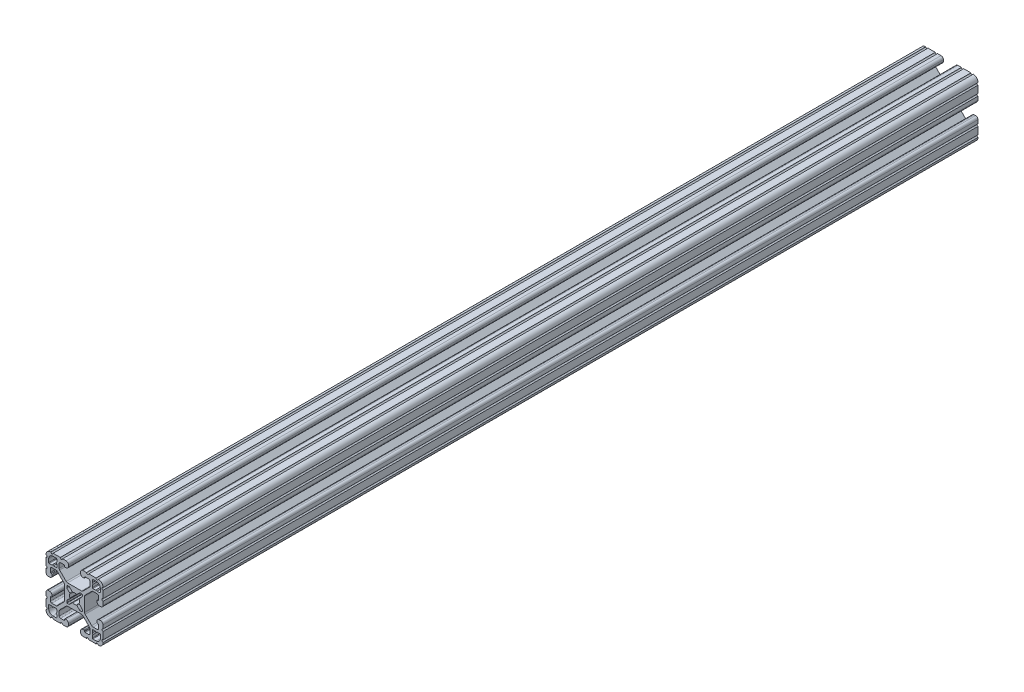
SolidWorks part; units mm, degrees
ref_plane "Front Plane" through (0, 0, 0) normal (0, 0, 1) x (1, 0, 0)
ref_plane "Top Plane" through (0, 0, 0) normal (0, 1, 0) x (1, 0, 0)
ref_plane "Right Plane" through (0, 0, 0) normal (1, 0, 0) x (0, 0, -1)
ref_plane "Plane1" through (0, 0, -2322.576) normal (0, 0, -1) x (-1, 0, 0)
sketch "Sketch1" plane through (0, 0, -2322.576) normal (0, 0, -1) x (-1, 0, 0)
  line L0 (17.2466, 14.4526) -> (17.2466, 12.2428)
  line L1 (16.8656, 11.8618) -> (15.0927, 11.8618)
  line L2 (15.0927, 11.8618) -> (14.5542, 12.4003)
  line L3 (14.5542, 12.4003) -> (14.0157, 11.8618)
  line L4 (14.0157, 11.8618) -> (12.2428, 11.8618)
  line L5 (11.8618, 12.2428) -> (11.8618, 14.0157)
  line L6 (11.8618, 14.0157) -> (12.4003, 14.5542)
  line L7 (12.4003, 14.5542) -> (11.8618, 15.0927)
  line L8 (11.8618, 15.0927) -> (11.8618, 16.8656)
  line L9 (12.2428, 17.2466) -> (14.4526, 17.2466)
  line L10 (17.2466, -12.2428) -> (17.2466, -14.4526)
  line L11 (14.4526, -17.2466) -> (12.2428, -17.2466)
  line L12 (11.8618, -16.8656) -> (11.8618, -15.0927)
  line L13 (11.8618, -15.0927) -> (12.4003, -14.5542)
  line L14 (12.4003, -14.5542) -> (11.8618, -14.0157)
  line L15 (11.8618, -14.0157) -> (11.8618, -12.2428)
  line L16 (12.2428, -11.8618) -> (14.0157, -11.8618)
  line L17 (14.0157, -11.8618) -> (14.5542, -12.4003)
  line L18 (14.5542, -12.4003) -> (15.0927, -11.8618)
  line L19 (15.0927, -11.8618) -> (16.8656, -11.8618)
  line L20 (5.1689, -3.9207) -> (5.1689, -4.9149)
  line L21 (4.9149, -5.1689) -> (3.9207, -5.1689)
  line L22 (3.2921, -4.9085) -> (1.5823, -3.1988)
  line L23 (-1.5823, -3.1988) -> (-3.2921, -4.9085)
  line L24 (-3.9207, -5.1689) -> (-4.9149, -5.1689)
  line L25 (-5.1689, -4.9149) -> (-5.1689, -3.9207)
  line L26 (-4.9085, -3.2921) -> (-3.1988, -1.5823)
  line L27 (-3.1988, 1.5823) -> (-4.9085, 3.2921)
  line L28 (-5.1689, 3.9207) -> (-5.1689, 4.9149)
  line L29 (-4.9149, 5.1689) -> (-3.9207, 5.1689)
  line L30 (-3.2921, 4.9085) -> (-1.5823, 3.1988)
  line L31 (1.5823, 3.1988) -> (3.2921, 4.9085)
  line L32 (3.9207, 5.1689) -> (4.9149, 5.1689)
  line L33 (5.1689, 4.9149) -> (5.1689, 3.9207)
  line L34 (4.9085, 3.2921) -> (3.1988, 1.5823)
  line L35 (3.1988, -1.5823) -> (4.9085, -3.2921)
  line L36 (-11.8618, -12.2428) -> (-11.8618, -14.0157)
  line L37 (-11.8618, -14.0157) -> (-12.4003, -14.5542)
  line L38 (-12.4003, -14.5542) -> (-11.8618, -15.0927)
  line L39 (-11.8618, -15.0927) -> (-11.8618, -16.8656)
  line L40 (-12.2428, -17.2466) -> (-14.4526, -17.2466)
  line L41 (-17.2466, -14.4526) -> (-17.2466, -12.2428)
  line L42 (-16.8656, -11.8618) -> (-15.0927, -11.8618)
  line L43 (-15.0927, -11.8618) -> (-14.5542, -12.4003)
  line L44 (-14.5542, -12.4003) -> (-14.0157, -11.8618)
  line L45 (-14.0157, -11.8618) -> (-12.2428, -11.8618)
  line L46 (-11.8618, 16.8656) -> (-11.8618, 15.0927)
  line L47 (-11.8618, 15.0927) -> (-12.4003, 14.5542)
  line L48 (-12.4003, 14.5542) -> (-11.8618, 14.0157)
  line L49 (-11.8618, 14.0157) -> (-11.8618, 12.2428)
  line L50 (-12.2428, 11.8618) -> (-14.0157, 11.8618)
  line L51 (-14.0157, 11.8618) -> (-14.5542, 12.4003)
  line L52 (-14.5542, 12.4003) -> (-15.0927, 11.8618)
  line L53 (-15.0927, 11.8618) -> (-16.8656, 11.8618)
  line L54 (-17.2466, 12.2428) -> (-17.2466, 14.4526)
  line L55 (-14.4526, 17.2466) -> (-12.2428, 17.2466)
  line L56 (19.05, -14.3256) -> (19.05, -9.4996)
  line L57 (19.05, -7.9756) -> (19.05, -5.6388)
  line L58 (17.4752, -4.064) -> (16.5608, -4.064)
  line L59 (14.986, -5.6388) -> (14.986, -6.35)
  line L60 (15.367, -6.731) -> (15.6972, -6.731)
  line L61 (16.0782, -7.112) -> (16.0782, -9.398)
  line L62 (15.1892, -10.287) -> (12.3756, -10.287)
  line L63 (11.4776, -9.915) -> (7.1157, -5.5531)
  line L64 (6.7437, -4.6551) -> (6.7437, 4.6551)
  line L65 (7.1157, 5.5531) -> (11.4776, 9.915)
  line L66 (12.3756, 10.287) -> (15.1892, 10.287)
  line L67 (16.0782, 9.398) -> (16.0782, 7.112)
  line L68 (15.6972, 6.731) -> (15.367, 6.731)
  line L69 (14.986, 6.35) -> (14.986, 5.6388)
  line L70 (16.5608, 4.064) -> (17.4752, 4.064)
  line L71 (19.05, 5.6388) -> (19.05, 7.9756)
  line L72 (19.05, 9.4996) -> (19.05, 14.3256)
  line L73 (14.3256, 19.05) -> (9.4996, 19.05)
  line L74 (7.9756, 19.05) -> (5.6388, 19.05)
  line L75 (4.064, 17.4752) -> (4.064, 16.5608)
  line L76 (5.6388, 14.986) -> (6.35, 14.986)
  line L77 (6.731, 15.367) -> (6.731, 15.6972)
  line L78 (7.112, 16.0782) -> (9.398, 16.0782)
  line L79 (10.287, 15.1892) -> (10.287, 12.3756)
  line L80 (9.915, 11.4776) -> (5.5531, 7.1157)
  line L81 (4.6551, 6.7437) -> (-4.6551, 6.7437)
  line L82 (-5.5531, 7.1157) -> (-9.915, 11.4776)
  line L83 (-10.287, 12.3756) -> (-10.287, 15.1892)
  line L84 (-9.398, 16.0782) -> (-7.112, 16.0782)
  line L85 (-6.731, 15.6972) -> (-6.731, 15.367)
  line L86 (-6.35, 14.986) -> (-5.6388, 14.986)
  line L87 (-4.064, 16.5608) -> (-4.064, 17.4752)
  line L88 (-5.6388, 19.05) -> (-7.9756, 19.05)
  line L89 (-9.4996, 19.05) -> (-14.3256, 19.05)
  line L90 (-19.05, 14.3256) -> (-19.05, 9.4996)
  line L91 (-19.05, 7.9756) -> (-19.05, 5.6388)
  line L92 (-17.4752, 4.064) -> (-16.5608, 4.064)
  line L93 (-14.986, 5.6388) -> (-14.986, 6.35)
  line L94 (-15.367, 6.731) -> (-15.6972, 6.731)
  line L95 (-16.0782, 7.112) -> (-16.0782, 9.398)
  line L96 (-15.1892, 10.287) -> (-12.3756, 10.287)
  line L97 (-11.4776, 9.915) -> (-7.1157, 5.5531)
  line L98 (-6.7437, 4.6551) -> (-6.7437, -4.6551)
  line L99 (-7.1157, -5.5531) -> (-11.4776, -9.915)
  line L100 (-12.3756, -10.287) -> (-15.1892, -10.287)
  line L101 (-16.0782, -9.398) -> (-16.0782, -7.112)
  line L102 (-15.6972, -6.731) -> (-15.367, -6.731)
  line L103 (-14.986, -6.35) -> (-14.986, -5.6388)
  line L104 (-16.5608, -4.064) -> (-17.4752, -4.064)
  line L105 (-19.05, -5.6388) -> (-19.05, -7.9756)
  line L106 (-19.05, -9.4996) -> (-19.05, -14.3256)
  line L107 (-14.3256, -19.05) -> (-9.4996, -19.05)
  line L108 (-7.9756, -19.05) -> (-5.6388, -19.05)
  line L109 (-4.064, -17.4752) -> (-4.064, -16.5608)
  line L110 (-5.6388, -14.986) -> (-6.35, -14.986)
  line L111 (-6.731, -15.367) -> (-6.731, -15.6972)
  line L112 (-7.112, -16.0782) -> (-9.398, -16.0782)
  line L113 (-10.287, -15.1892) -> (-10.287, -12.3756)
  line L114 (-9.915, -11.4776) -> (-5.5531, -7.1157)
  line L115 (-4.6551, -6.7437) -> (4.6551, -6.7437)
  line L116 (5.5531, -7.1157) -> (9.915, -11.4776)
  line L117 (10.287, -12.3756) -> (10.287, -15.1892)
  line L118 (9.398, -16.0782) -> (7.112, -16.0782)
  line L119 (6.731, -15.6972) -> (6.731, -15.367)
  line L120 (6.35, -14.986) -> (5.6388, -14.986)
  line L121 (4.064, -16.5608) -> (4.064, -17.4752)
  line L122 (5.6388, -19.05) -> (7.9756, -19.05)
  line L123 (9.4996, -19.05) -> (14.3256, -19.05)
  arc A0 (17.2466, 12.2428) -> (16.8656, 11.8618) centre (16.8656, 12.2428) cw
  arc A1 (12.2428, 11.8618) -> (11.8618, 12.2428) centre (12.2428, 12.2428) cw
  arc A2 (11.8618, 16.8656) -> (12.2428, 17.2466) centre (12.2428, 16.8656) cw
  arc A3 (14.4526, 17.2466) -> (17.2466, 14.4526) centre (14.4526, 14.4526) cw
  arc A4 (17.2466, -14.4526) -> (14.4526, -17.2466) centre (14.4526, -14.4526) cw
  arc A5 (12.2428, -17.2466) -> (11.8618, -16.8656) centre (12.2428, -16.8656) cw
  arc A6 (11.8618, -12.2428) -> (12.2428, -11.8618) centre (12.2428, -12.2428) cw
  arc A7 (16.8656, -11.8618) -> (17.2466, -12.2428) centre (16.8656, -12.2428) cw
  arc A8 (5.1689, -4.9149) -> (4.9149, -5.1689) centre (4.9149, -4.9149) cw
  arc A9 (3.9207, -5.1689) -> (3.2921, -4.9085) centre (3.9207, -4.2799) cw
  arc A10 (1.5823, -3.1988) -> (1.178, -3.1119) centre (1.3129, -3.4682) ccw
  arc A11 (1.178, -3.1119) -> (-1.178, -3.1119) centre (0, 0) cw
  arc A12 (-1.178, -3.1119) -> (-1.5823, -3.1988) centre (-1.3129, -3.4682) ccw
  arc A13 (-3.2921, -4.9085) -> (-3.9207, -5.1689) centre (-3.9207, -4.2799) cw
  arc A14 (-4.9149, -5.1689) -> (-5.1689, -4.9149) centre (-4.9149, -4.9149) cw
  arc A15 (-5.1689, -3.9207) -> (-4.9085, -3.2921) centre (-4.2799, -3.9207) cw
  arc A16 (-3.1988, -1.5823) -> (-3.1119, -1.178) centre (-3.4682, -1.3129) ccw
  arc A17 (-3.1119, -1.178) -> (-3.1119, 1.178) centre (0, 0) cw
  arc A18 (-3.1119, 1.178) -> (-3.1988, 1.5823) centre (-3.4682, 1.3129) ccw
  arc A19 (-4.9085, 3.2921) -> (-5.1689, 3.9207) centre (-4.2799, 3.9207) cw
  arc A20 (-5.1689, 4.9149) -> (-4.9149, 5.1689) centre (-4.9149, 4.9149) cw
  arc A21 (-3.9207, 5.1689) -> (-3.2921, 4.9085) centre (-3.9207, 4.2799) cw
  arc A22 (-1.5823, 3.1988) -> (-1.178, 3.1119) centre (-1.3129, 3.4682) ccw
  arc A23 (-1.178, 3.1119) -> (1.178, 3.1119) centre (0, 0) cw
  arc A24 (1.178, 3.1119) -> (1.5823, 3.1988) centre (1.3129, 3.4682) ccw
  arc A25 (3.2921, 4.9085) -> (3.9207, 5.1689) centre (3.9207, 4.2799) cw
  arc A26 (4.9149, 5.1689) -> (5.1689, 4.9149) centre (4.9149, 4.9149) cw
  arc A27 (5.1689, 3.9207) -> (4.9085, 3.2921) centre (4.2799, 3.9207) cw
  arc A28 (3.1988, 1.5823) -> (3.1119, 1.178) centre (3.4682, 1.3129) ccw
  arc A29 (3.1119, 1.178) -> (3.1119, -1.178) centre (0, 0) cw
  arc A30 (3.1119, -1.178) -> (3.1988, -1.5823) centre (3.4682, -1.3129) ccw
  arc A31 (4.9085, -3.2921) -> (5.1689, -3.9207) centre (4.2799, -3.9207) cw
  arc A32 (-11.8618, -16.8656) -> (-12.2428, -17.2466) centre (-12.2428, -16.8656) cw
  arc A33 (-14.4526, -17.2466) -> (-17.2466, -14.4526) centre (-14.4526, -14.4526) cw
  arc A34 (-17.2466, -12.2428) -> (-16.8656, -11.8618) centre (-16.8656, -12.2428) cw
  arc A35 (-12.2428, -11.8618) -> (-11.8618, -12.2428) centre (-12.2428, -12.2428) cw
  arc A36 (-12.2428, 17.2466) -> (-11.8618, 16.8656) centre (-12.2428, 16.8656) cw
  arc A37 (-11.8618, 12.2428) -> (-12.2428, 11.8618) centre (-12.2428, 12.2428) cw
  arc A38 (-16.8656, 11.8618) -> (-17.2466, 12.2428) centre (-16.8656, 12.2428) cw
  arc A39 (-17.2466, 14.4526) -> (-14.4526, 17.2466) centre (-14.4526, 14.4526) cw
  arc A40 (19.05, -9.4996) -> (19.05, -7.9756) centre (19.05, -8.7376) cw
  arc A41 (19.05, -5.6388) -> (17.4752, -4.064) centre (17.4752, -5.6388) ccw
  arc A42 (16.5608, -4.064) -> (14.986, -5.6388) centre (16.5608, -5.6388) ccw
  arc A43 (14.986, -6.35) -> (15.367, -6.731) centre (15.367, -6.35) ccw
  arc A44 (15.6972, -6.731) -> (16.0782, -7.112) centre (15.6972, -7.112) cw
  arc A45 (16.0782, -9.398) -> (15.1892, -10.287) centre (15.1892, -9.398) cw
  arc A46 (12.3756, -10.287) -> (11.4776, -9.915) centre (12.3756, -9.017) cw
  arc A47 (7.1157, -5.5531) -> (6.7437, -4.6551) centre (8.0137, -4.6551) cw
  arc A48 (6.7437, 4.6551) -> (7.1157, 5.5531) centre (8.0137, 4.6551) cw
  arc A49 (11.4776, 9.915) -> (12.3756, 10.287) centre (12.3756, 9.017) cw
  arc A50 (15.1892, 10.287) -> (16.0782, 9.398) centre (15.1892, 9.398) cw
  arc A51 (16.0782, 7.112) -> (15.6972, 6.731) centre (15.6972, 7.112) cw
  arc A52 (15.367, 6.731) -> (14.986, 6.35) centre (15.367, 6.35) ccw
  arc A53 (14.986, 5.6388) -> (16.5608, 4.064) centre (16.5608, 5.6388) ccw
  arc A54 (17.4752, 4.064) -> (19.05, 5.6388) centre (17.4752, 5.6388) ccw
  arc A55 (19.05, 7.9756) -> (19.05, 9.4996) centre (19.05, 8.7376) cw
  arc A56 (19.05, 14.3256) -> (19.0499, 15.8496) centre (19.05, 15.0876) cw
  arc A57 (19.0499, 15.8496) -> (15.8496, 19.0499) centre (15.875, 15.875) ccw
  arc A58 (15.8496, 19.0499) -> (14.3256, 19.05) centre (15.0876, 19.05) cw
  arc A59 (9.4996, 19.05) -> (7.9756, 19.05) centre (8.7376, 19.05) cw
  arc A60 (5.6388, 19.05) -> (4.064, 17.4752) centre (5.6388, 17.4752) ccw
  arc A61 (4.064, 16.5608) -> (5.6388, 14.986) centre (5.6388, 16.5608) ccw
  arc A62 (6.35, 14.986) -> (6.731, 15.367) centre (6.35, 15.367) ccw
  arc A63 (6.731, 15.6972) -> (7.112, 16.0782) centre (7.112, 15.6972) cw
  arc A64 (9.398, 16.0782) -> (10.287, 15.1892) centre (9.398, 15.1892) cw
  arc A65 (10.287, 12.3756) -> (9.915, 11.4776) centre (9.017, 12.3756) cw
  arc A66 (5.5531, 7.1157) -> (4.6551, 6.7437) centre (4.6551, 8.0137) cw
  arc A67 (-4.6551, 6.7437) -> (-5.5531, 7.1157) centre (-4.6551, 8.0137) cw
  arc A68 (-9.915, 11.4776) -> (-10.287, 12.3756) centre (-9.017, 12.3756) cw
  arc A69 (-10.287, 15.1892) -> (-9.398, 16.0782) centre (-9.398, 15.1892) cw
  arc A70 (-7.112, 16.0782) -> (-6.731, 15.6972) centre (-7.112, 15.6972) cw
  arc A71 (-6.731, 15.367) -> (-6.35, 14.986) centre (-6.35, 15.367) ccw
  arc A72 (-5.6388, 14.986) -> (-4.064, 16.5608) centre (-5.6388, 16.5608) ccw
  arc A73 (-4.064, 17.4752) -> (-5.6388, 19.05) centre (-5.6388, 17.4752) ccw
  arc A74 (-7.9756, 19.05) -> (-9.4996, 19.05) centre (-8.7376, 19.05) cw
  arc A75 (-14.3256, 19.05) -> (-15.8496, 19.0499) centre (-15.0876, 19.05) cw
  arc A76 (-15.8496, 19.0499) -> (-19.0499, 15.8496) centre (-15.875, 15.875) ccw
  arc A77 (-19.0499, 15.8496) -> (-19.05, 14.3256) centre (-19.05, 15.0876) cw
  arc A78 (-19.05, 9.4996) -> (-19.05, 7.9756) centre (-19.05, 8.7376) cw
  arc A79 (-19.05, 5.6388) -> (-17.4752, 4.064) centre (-17.4752, 5.6388) ccw
  arc A80 (-16.5608, 4.064) -> (-14.986, 5.6388) centre (-16.5608, 5.6388) ccw
  arc A81 (-14.986, 6.35) -> (-15.367, 6.731) centre (-15.367, 6.35) ccw
  arc A82 (-15.6972, 6.731) -> (-16.0782, 7.112) centre (-15.6972, 7.112) cw
  arc A83 (-16.0782, 9.398) -> (-15.1892, 10.287) centre (-15.1892, 9.398) cw
  arc A84 (-12.3756, 10.287) -> (-11.4776, 9.915) centre (-12.3756, 9.017) cw
  arc A85 (-7.1157, 5.5531) -> (-6.7437, 4.6551) centre (-8.0137, 4.6551) cw
  arc A86 (-6.7437, -4.6551) -> (-7.1157, -5.5531) centre (-8.0137, -4.6551) cw
  arc A87 (-11.4776, -9.915) -> (-12.3756, -10.287) centre (-12.3756, -9.017) cw
  arc A88 (-15.1892, -10.287) -> (-16.0782, -9.398) centre (-15.1892, -9.398) cw
  arc A89 (-16.0782, -7.112) -> (-15.6972, -6.731) centre (-15.6972, -7.112) cw
  arc A90 (-15.367, -6.731) -> (-14.986, -6.35) centre (-15.367, -6.35) ccw
  arc A91 (-14.986, -5.6388) -> (-16.5608, -4.064) centre (-16.5608, -5.6388) ccw
  arc A92 (-17.4752, -4.064) -> (-19.05, -5.6388) centre (-17.4752, -5.6388) ccw
  arc A93 (-19.05, -7.9756) -> (-19.05, -9.4996) centre (-19.05, -8.7376) cw
  arc A94 (-19.05, -14.3256) -> (-19.0499, -15.8496) centre (-19.05, -15.0876) cw
  arc A95 (-19.0499, -15.8496) -> (-15.8496, -19.0499) centre (-15.875, -15.875) ccw
  arc A96 (-15.8496, -19.0499) -> (-14.3256, -19.05) centre (-15.0876, -19.05) cw
  arc A97 (-9.4996, -19.05) -> (-7.9756, -19.05) centre (-8.7376, -19.05) cw
  arc A98 (-5.6388, -19.05) -> (-4.064, -17.4752) centre (-5.6388, -17.4752) ccw
  arc A99 (-4.064, -16.5608) -> (-5.6388, -14.986) centre (-5.6388, -16.5608) ccw
  arc A100 (-6.35, -14.986) -> (-6.731, -15.367) centre (-6.35, -15.367) ccw
  arc A101 (-6.731, -15.6972) -> (-7.112, -16.0782) centre (-7.112, -15.6972) cw
  arc A102 (-9.398, -16.0782) -> (-10.287, -15.1892) centre (-9.398, -15.1892) cw
  arc A103 (-10.287, -12.3756) -> (-9.915, -11.4776) centre (-9.017, -12.3756) cw
  arc A104 (-5.5531, -7.1157) -> (-4.6551, -6.7437) centre (-4.6551, -8.0137) cw
  arc A105 (4.6551, -6.7437) -> (5.5531, -7.1157) centre (4.6551, -8.0137) cw
  arc A106 (9.915, -11.4776) -> (10.287, -12.3756) centre (9.017, -12.3756) cw
  arc A107 (10.287, -15.1892) -> (9.398, -16.0782) centre (9.398, -15.1892) cw
  arc A108 (7.112, -16.0782) -> (6.731, -15.6972) centre (7.112, -15.6972) cw
  arc A109 (6.731, -15.367) -> (6.35, -14.986) centre (6.35, -15.367) ccw
  arc A110 (5.6388, -14.986) -> (4.064, -16.5608) centre (5.6388, -16.5608) ccw
  arc A111 (4.064, -17.4752) -> (5.6388, -19.05) centre (5.6388, -17.4752) ccw
  arc A112 (7.9756, -19.05) -> (9.4996, -19.05) centre (8.7376, -19.05) cw
  arc A113 (14.3256, -19.05) -> (15.8496, -19.0499) centre (15.0876, -19.05) cw
  arc A114 (15.8496, -19.0499) -> (19.0499, -15.8496) centre (15.875, -15.875) ccw
  arc A115 (19.0499, -15.8496) -> (19.05, -14.3256) centre (19.05, -15.0876) cw
extrude "Boss-Extrude1" add sketch "Sketch1" against normal blind 584.2
